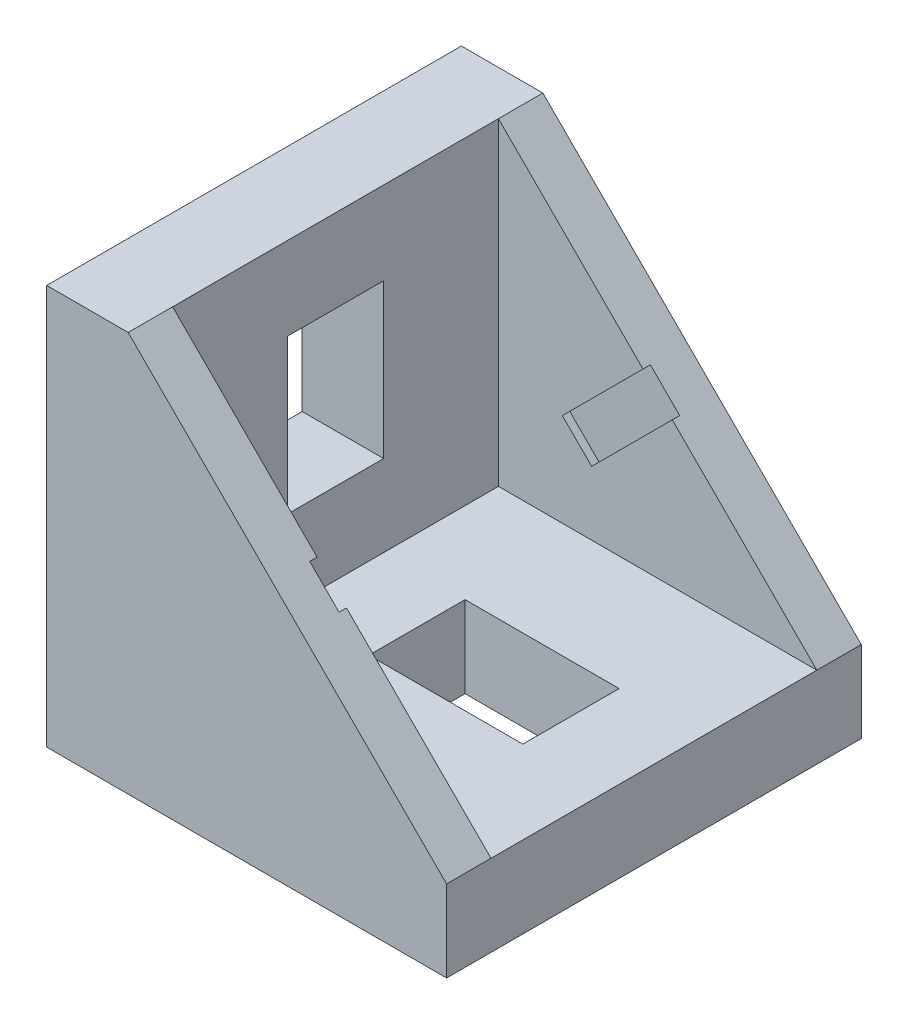
SolidWorks part; units mm, degrees
material "6063-T6"
ref_plane "Plan de face" through (0, 0, 0) normal (0, 0, 1) x (1, 0, 0)
ref_plane "Plan de dessus" through (0, 0, 0) normal (0, 1, 0) x (1, 0, 0)
ref_plane "Plan de droite" through (0, 0, 0) normal (1, 0, 0) x (0, 0, -1)
sketch "Esquisse1" plane through (0, 0, 0) normal (0, 0, 1) x (1, 0, 0)
  line L0 (0, 27) -> (0, 0)
  line L1 (-66.0678, 0) -> (83.392, 0) construction
  line L2 (0, 0) -> (60.9359, 60.9359) construction
  line L3 (0, 27) -> (5.5, 27)
  line L4 (5.5, 27) -> (27, 5.5)
  line L5 (27, 0) -> (27, 5.5)
  line L6 (27, 0) -> (0, 0)
  point P9 (16.25, 16.25)
  dimension "D1" = 45
  dimension "D2" = 27
  dimension "D3" = 5.5
extrude "Boss.-Extru.1" add sketch "Esquisse1" along normal blind 28
sketch "Esquisse2" plane through (0, 27, 0) normal (0, 1, 0) x (1, 0, 0)
  line L0 (5.5, -28) -> (5.5, 0) construction
  line L1 (5.5, -3) -> (27, -3)
  line L2 (5.5, -3) -> (5.5, -25)
  line L3 (5.5, -25) -> (27, -25)
  line L4 (27, -3) -> (27, -25)
  line L5 (27, -28) -> (27, 0) construction
  line L6 (27, 0) -> (5.5, 0) construction
  line L7 (27, -28) -> (5.5, -28) construction
  dimension "D1" = 3
  dimension "D2" = 3
extrude "Enlèv. mat.-Extru.1" cut sketch "Esquisse2" against normal up to vertex (21.5 mm away) up to point (27, 5.5, 28)
sketch "Esquisse3" plane through (5.5, 0, 0) normal (1, 0, 0) x (0, 0, -1)
  line L0 (-3, 27) -> (-25, 27) construction
  line L5 (-14, 27) -> (-14, 5.5) construction
  line L6 (-3, 5.5) -> (-25, 5.5) construction
  line L8 (-17.25, 21.4) -> (-10.75, 21.4)
  line L9 (-17.25, 21.4) -> (-17.25, 11)
  line L10 (-17.25, 11) -> (-10.75, 11)
  line L11 (-10.75, 21.4) -> (-10.75, 11)
  line L12 (-17.25, 21.4) -> (-10.75, 11) construction
  line L13 (-17.25, 11) -> (-10.75, 21.4) construction
  point P0 (-14, 16.2)
  dimension "D1" = 5.6
  dimension "D2" = 10.4
  dimension "D3" = 6.5
extrude "Enlèv. mat.-Extru.2" cut sketch "Esquisse3" against normal blind 6.9
sketch "Esquisse4" plane through (0, 5.5, 0) normal (0, 1, 0) x (1, 0, 0)
  line L0 (27, -14) -> (5.5, -14) construction
  line L1 (27, -25) -> (27, -3) construction
  line L3 (11, -17.25) -> (21.4, -17.25)
  line L4 (11, -17.25) -> (11, -10.75)
  line L5 (11, -10.75) -> (21.4, -10.75)
  line L6 (21.4, -17.25) -> (21.4, -10.75)
  line L7 (11, -17.25) -> (21.4, -10.75) construction
  line L8 (11, -10.75) -> (21.4, -17.25) construction
  point P5 (16.2, -14)
  dimension "D1" = 5.6
  dimension "D2" = 10.4
  dimension "D3" = 6.5
extrude "Enlèv. mat.-Extru.3" cut sketch "Esquisse4" against normal blind 18
sketch "Esquisse5" plane through (16.25, 16.25, 0) normal (0.7071, 0.7071, 0) x (0, 0, -1)
  line L0 (-28, 0) -> (0, 0) construction
  line L1 (-28, -15.2028) -> (-28, 15.2028) construction
  line L2 (-25, 0) -> (-25, 15.2028) construction
  line L3 (-25.5, -1.4) -> (-25, -1.4)
  line L4 (-25.5, -1.4) -> (-25.5, 1.4)
  line L5 (-25.5, 1.4) -> (-25, 1.4)
  line L6 (-25, -1.4) -> (-25, 1.4)
  line L7 (-25.5, -1.4) -> (-25, 1.4) construction
  line L8 (-25.5, 1.4) -> (-25, -1.4) construction
  line L9 (-14, 19.0919) -> (-14, -19.0919) construction
  line L10 (-28, 19.0919) -> (0, 19.0919) construction
  line L11 (-28, -19.0919) -> (0, -19.0919) construction
  line L12 (-2.5, 1.4) -> (-3, -1.4) construction
  line L13 (-2.5, -1.4) -> (-3, 1.4) construction
  line L14 (-3, -1.4) -> (-3, 1.4)
  line L15 (-2.5, 1.4) -> (-3, 1.4)
  line L16 (-2.5, -1.4) -> (-2.5, 1.4)
  line L17 (-2.5, -1.4) -> (-3, -1.4)
  point P5 (-25.25, 0)
  point P22 (-2.75, 0)
  dimension "D1" = 0.5
  dimension "D2" = 2.8
extrude "Enlèv. mat.-Extru.4" cut sketch "Esquisse5" against normal blind 7.7
ref_plane "Plan1" through (0, 0, 14) normal (0, 0, 1) x (1, 0, 0)
sketch "Esquisse6" plane through (0, 0, 14) normal (0, 0, 1) x (1, 0, 0)
  line L0 (0, 27) -> (-2.4749, 24.5251)
  line L1 (0, 27) -> (1.0607, 25.9393)
  line L2 (-2.4749, 24.5251) -> (-1.4142, 23.4645)
  line L3 (1.0607, 25.9393) -> (-1.4142, 23.4645)
  line L4 (0, 27) -> (0, 0) construction
  line L5 (0, 4.1719) -> (-2.4749, 1.6971)
  line L6 (0, 4.1719) -> (1.0607, 3.1113)
  line L7 (-2.4749, 1.6971) -> (-1.4142, 0.6364)
  line L8 (1.0607, 3.1113) -> (-1.4142, 0.6364)
  line L9 (0, 0) -> (27, 0) construction
  line L10 (3.1113, 1.0607) -> (0.6364, -1.4142)
  line L11 (3.1113, 1.0607) -> (4.1719, 0)
  line L12 (0.6364, -1.4142) -> (1.6971, -2.4749)
  line L13 (4.1719, 0) -> (1.6971, -2.4749)
  line L14 (25.9393, 1.0607) -> (23.4645, -1.4142)
  line L15 (25.9393, 1.0607) -> (27, 0)
  line L16 (23.4645, -1.4142) -> (24.5251, -2.4749)
  line L17 (27, 0) -> (24.5251, -2.4749)
  line L18 (0, 0) -> (16.25, 16.25) construction
  line L19 (27, 5.5) -> (5.5, 27) construction
  dimension "D1" = 3.5
  dimension "D2" = 1.5
  dimension "D3" = 45
  dimension "D4" = 3.5
  dimension "D5" = 1.5
  dimension "D6" = 2.95
  dimension "D7" = 2.95
  dimension "D8" = 3.5
  dimension "D9" = 1.5
  dimension "D10" = 3.5
  dimension "D11" = 1.5
  dimension "D12" = 45
  dimension "D13" = 45
  dimension "D14" = 45
extrude "Boss.-Extru.2" add sketch "Esquisse6" along normal blind 3.9 and the other way blind 3.9
